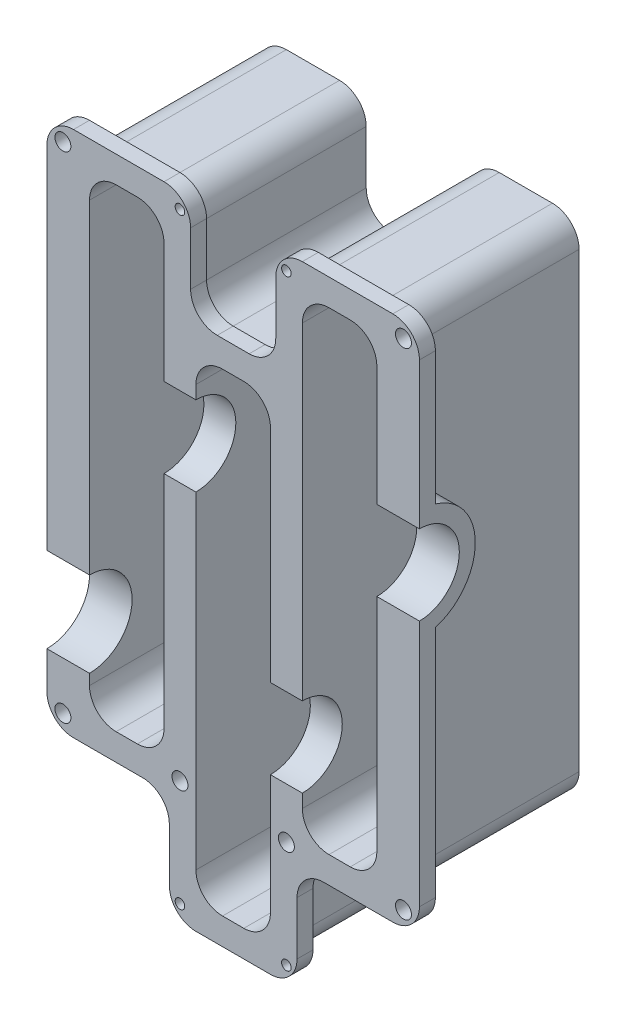
SolidWorks part; units mm, degrees
ref_plane "Front Plane" through (0, 0, 0) normal (0, 0, 1) x (1, 0, 0)
ref_plane "Top Plane" through (0, 0, 0) normal (0, 1, 0) x (1, 0, 0)
ref_plane "Right Plane" through (0, 0, 0) normal (1, 0, 0) x (0, 0, -1)
sketch "Sketch1" plane through (0, 0, 0) normal (0, 0, 1) x (1, 0, 0)
  line L1 (-35, 59.5) -> (35, 59.5)
  line L2 (-35, 59.5) -> (-35, -59.5)
  line L3 (-35, -59.5) -> (35, -59.5)
  line L4 (35, 59.5) -> (35, -59.5)
  line L5 (-35, 59.5) -> (35, -59.5) construction
  line L6 (-35, -59.5) -> (35, 59.5) construction
  point P0 (0, 0)
  dimension "D1" = 119
  dimension "D2" = 70
extrude "Boss-Extrude1" add sketch "Sketch1" along normal blind 35
sketch "Sketch2" plane through (-35, 0, 0) normal (-1, 0, 0) x (0, 0, 1)
  line L0 (35, 59.5) -> (35, -59.5) construction
  line L1 (35, -59.5) -> (0, -59.5) construction
  circle A0 centre (35, -19.5) radius 8
  dimension "D2" = 16
  dimension "D1" = 40
extrude "Cut-Extrude1" cut sketch "Sketch2" against normal blind 8
sketch "Sketch3" plane through (0, 0, 35) normal (0, 0, 1) x (1, 0, 0)
  line L0 (-35, 59.5) -> (-35, -11.5) construction
  line L1 (-27, 54.5) -> (-13, 54.5)
  line L2 (-27, 54.5) -> (-27, -34.5)
  line L3 (-27, -34.5) -> (-13, -34.5)
  line L4 (-13, 54.5) -> (-13, 27)
  line L5 (-7, 34.5) -> (7, 34.5)
  line L6 (-7, 34.5) -> (-7, 27)
  line L7 (-7, -54.5) -> (7, -54.5)
  line L8 (7, 34.5) -> (7, -12)
  line L9 (13, 54.5) -> (27, 54.5)
  line L10 (13, 54.5) -> (13, -12)
  line L11 (13, -34.5) -> (27, -34.5)
  line L12 (27, 54.5) -> (27, -34.5)
  line L13 (-35, -19.5) -> (40.8118, -19.5) construction
  line L14 (-35, -11.5) -> (-35, -27.5) construction
  line L15 (-41.2819, 19.5) -> (46.0892, 19.5) construction
  line L16 (-7, 27) -> (-13, 27)
  line L17 (-7, 12) -> (-13, 12)
  line L18 (-7, 12) -> (-7, -54.5)
  line L19 (-13, 12) -> (-13, -34.5)
  line L20 (7, -27) -> (13, -27)
  line L21 (7, -12) -> (13, -12)
  line L22 (13, -27) -> (13, -34.5)
  line L23 (7, -27) -> (7, -54.5)
  dimension "D1" = 8
  dimension "D2" = 14
  dimension "D3" = 6
  dimension "D4" = 6
  dimension "D5" = 39
  dimension "D6" = 15
  dimension "D7" = 89
  dimension "D8" = 15
  dimension "D9" = 7.5
  dimension "D10" = 15
  dimension "D11" = 7.5
  dimension "D12" = 15
  dimension "D13" = 89
extrude "Cut-Extrude2" cut sketch "Sketch3" against normal blind 32
sketch "Sketch4" plane through (35, 0, 0) normal (1, 0, 0) x (0, 0, -1)
  line L0 (-35, -59.5) -> (-35, 59.5) construction
  line L1 (-35, -59.5) -> (0, -59.5) construction
  circle A0 centre (-35, 19.5) radius 7.5
  dimension "D1" = 15
  dimension "D2" = 79
extrude "Cut-Extrude3" cut sketch "Sketch4" against normal blind 8
sketch "Sketch5" plane through (0, 0, 35) normal (0, 0, 1) x (1, 0, 0)
  line L0 (35, 59.5) -> (-35, 59.5) construction
  line L1 (8, 59.5) -> (-8, 59.5)
  line L2 (8, 59.5) -> (8, 39.5)
  line L3 (8, 39.5) -> (-8, 39.5)
  line L4 (-8, 59.5) -> (-8, 39.5)
  line L5 (-35, -27.5) -> (-35, -59.5) construction
  line L6 (-35, -39.5) -> (-12, -39.5)
  line L7 (-35, -39.5) -> (-35, -59.5)
  line L8 (-35, -59.5) -> (-12, -59.5)
  line L9 (-12, -39.5) -> (-12, -59.5)
  line L10 (-35, -59.5) -> (35, -59.5) construction
  line L11 (35, -59.5) -> (35, 12) construction
  line L12 (12, -59.5) -> (35, -59.5)
  line L13 (12, -59.5) -> (12, -39.5)
  line L14 (12, -39.5) -> (35, -39.5)
  line L15 (35, -59.5) -> (35, -39.5)
  line L16 (13, -34.5) -> (27, -34.5) construction
  line L17 (7, -54.5) -> (7, -27) construction
  line L18 (-27, -34.5) -> (-13, -34.5) construction
  line L19 (-7, 12) -> (-7, -54.5) construction
  line L20 (-13, 27) -> (-13, 54.5) construction
  line L21 (13, 54.5) -> (13, -12) construction
  line L22 (7, 34.5) -> (-7, 34.5) construction
  dimension "D1" = 5
  dimension "D2" = 5
  dimension "D3" = 5
  dimension "D4" = 5
  dimension "D5" = 5
  dimension "D6" = 5
  dimension "D7" = 5
extrude "Cut-Extrude4" cut sketch "Sketch5" against normal through all
sketch "Sketch6" plane through (-35, 0, 0) normal (-1, 0, 0) x (0, 0, 1)
  line L2 (0, -39.5) -> (0, 59.5)
  line L3 (0, 59.5) -> (32, 59.5)
  line L4 (32, -30.083) -> (32, -39.5)
  line L5 (32, 59.5) -> (32, -8.917)
  line L6 (32, -30.083) -> (32, -39.5)
  line L7 (32, 59.5) -> (32, -8.917)
  line L8 (32, -39.5) -> (0, -39.5)
  arc A2 (32, -8.917) -> (32, -30.083) centre (35, -19.5) ccw
  arc A3 (32, -8.917) -> (32, -30.083) centre (35, -19.5) ccw
  dimension "D1" = 3
extrude "Cut-Extrude5" cut sketch "Sketch6" against normal blind 5
sketch "Sketch7" plane through (0, -39.5, 0) normal (0, -1, 0) x (1, 0, 0)
  line L0 (-12, 0) -> (-12, 35) construction
  line L1 (-30, 32) -> (-12, 32)
  line L2 (-30, 32) -> (-30, 0)
  line L3 (-30, 0) -> (-12, 0)
  line L4 (-12, 32) -> (-12, 0)
  line L5 (-12, 0) -> (-12, 35) construction
extrude "Cut-Extrude6" cut sketch "Sketch7" against normal blind 2
sketch "Sketch8" plane through (-12, 0, 0) normal (-1, 0, 0) x (0, 0, 1)
  line L0 (0, -59.5) -> (0, -37.5) construction
  line L1 (32, -37.5) -> (0, -37.5)
  line L2 (32, -37.5) -> (32, -59.5)
  line L3 (32, -59.5) -> (0, -59.5)
  line L4 (0, -37.5) -> (0, -59.5)
extrude "Cut-Extrude7" cut sketch "Sketch8" against normal blind 2
sketch "Sketch9" plane through (0, -59.5, 0) normal (0, -1, 0) x (1, 0, 0)
  line L1 (-10, 32) -> (12, 32)
  line L2 (-10, 32) -> (-10, 0)
  line L3 (-10, 0) -> (12, 0)
  line L4 (12, 32) -> (12, 0)
extrude "Cut-Extrude8" cut sketch "Sketch9" against normal blind 2
sketch "Sketch10" plane through (12, 0, 0) normal (1, 0, 0) x (0, 0, -1)
  line L1 (-32, -57.5) -> (0, -57.5)
  line L2 (-32, -57.5) -> (-32, -39.5)
  line L3 (-32, -39.5) -> (0, -39.5)
  line L4 (0, -57.5) -> (0, -39.5)
extrude "Cut-Extrude9" cut sketch "Sketch10" against normal blind 2
sketch "Sketch11" plane through (0, -39.5, 0) normal (0, -1, 0) x (1, 0, 0)
  line L1 (10, 32) -> (35, 32)
  line L2 (10, 32) -> (10, 0)
  line L3 (10, 0) -> (35, 0)
  line L4 (35, 32) -> (35, 0)
extrude "Cut-Extrude10" cut sketch "Sketch11" against normal blind 2
sketch "Sketch12" plane through (35, 0, 0) normal (1, 0, 0) x (0, 0, -1)
  line L2 (-32, 59.5) -> (0, 59.5)
  line L3 (0, 59.5) -> (0, -37.5)
  line L4 (-32, 29.5623) -> (-32, 59.5)
  line L5 (-32, -39.5) -> (-32, 9.4377)
  line L6 (-32, 29.5623) -> (-32, 59.5)
  line L7 (-32, -37.5) -> (-32, 9.4377)
  line L8 (0, -37.5) -> (-32, -37.5)
  arc A2 (-32, 9.4377) -> (-32, 29.5623) centre (-35, 19.5) ccw
  arc A3 (-32, 9.4377) -> (-32, 29.5623) centre (-35, 19.5) ccw
  dimension "D1" = 3
extrude "Cut-Extrude11" cut sketch "Sketch12" against normal blind 5
sketch "Sketch13" plane through (0, 59.5, 0) normal (0, 1, 0) x (1, 0, 0)
  line L1 (30, -32) -> (8, -32)
  line L2 (30, -32) -> (30, 0)
  line L3 (30, 0) -> (8, 0)
  line L4 (8, -32) -> (8, 0)
extrude "Cut-Extrude12" cut sketch "Sketch13" against normal blind 2
sketch "Sketch14" plane through (8, 0, 0) normal (-1, 0, 0) x (0, 0, 1)
  line L0 (32, -8.917) -> (32, 59.5) construction
  line L1 (32, 57.5) -> (0, 57.5)
  line L2 (32, 57.5) -> (32, 39.5)
  line L3 (32, 39.5) -> (0, 39.5)
  line L4 (0, 57.5) -> (0, 39.5)
  line L5 (0, 39.5) -> (35, 39.5) construction
  point P8 (0, 57.5)
extrude "Cut-Extrude17" cut sketch "Sketch14" against normal blind 2
sketch "Sketch18" plane through (0, 39.5, 0) normal (0, 1, 0) x (1, 0, 0)
  line L1 (-8, 0) -> (10, 0)
  line L2 (-8, 0) -> (-8, -32)
  line L3 (-8, -32) -> (10, -32)
  line L4 (10, 0) -> (10, -32)
extrude "Cut-Extrude18" cut sketch "Sketch18" against normal blind 2
sketch "Sketch20" plane through (-8, 0, 0) normal (1, 0, 0) x (0, 0, -1)
  line L1 (-32, 37.5) -> (0, 37.5)
  line L2 (-32, 37.5) -> (-32, 59.5)
  line L3 (-32, 59.5) -> (0, 59.5)
  line L4 (0, 37.5) -> (0, 59.5)
extrude "Cut-Extrude19" cut sketch "Sketch20" against normal blind 2
sketch "Sketch21" plane through (0, 59.5, 0) normal (0, 1, 0) x (1, 0, 0)
  line L1 (-10, -32) -> (-30, -32)
  line L2 (-10, -32) -> (-10, 0)
  line L3 (-10, 0) -> (-30, 0)
  line L4 (-30, -32) -> (-30, 0)
extrude "Cut-Extrude20" cut sketch "Sketch21" against normal blind 2
fillet "Fillet1" radius 5 12 edges at (-7, 34.5, 19) (7, 34.5, 19) (-13, -34.5, 19) (7, -54.5, 19) (27, -34.5, 19) (13, -34.5, 19) (-7, -54.5, 19) (-27, -34.5, 19) (13, 54.5, 19) (27, 54.5, 19) (-13, 54.5, 19) (-27, 54.5, 19)
fillet "Fillet2" radius 5 12 edges at (-35, -39.5, 33.5) (-12, -39.5, 33.5) (-12, -59.5, 33.5) (12, -59.5, 33.5) (12, -39.5, 33.5) (35, -39.5, 33.5) (10, -37.5, 16) (10, -57.5, 16) (-10, -57.5, 16) (-10, -37.5, 16) (-30, -37.5, 16) (30, -37.5, 16)
fillet "Fillet3" radius 5 12 edges at (30, 57.5, 16) (10, 57.5, 16) (10, 37.5, 16) (-10, 37.5, 16) (-10, 57.5, 16) (-30, 57.5, 16) (8, 39.5, 33.5) (-8, 39.5, 33.5) (-35, 59.5, 33.5) (-8, 59.5, 33.5) (8, 59.5, 33.5) (35, 59.5, 33.5)
sketch "Sketch23" plane through (0, 0, 35) normal (0, 0, 1) x (1, 0, 0)
  line L0 (-13, 59.5) -> (-30, 59.5) construction
  line L1 (-32, 56.5) -> (32, 56.5) construction
  line L2 (-32, 56.5) -> (-32, -36.5) construction
  line L3 (-32, -36.5) -> (32, -36.5) construction
  line L4 (32, 56.5) -> (32, -36.5) construction
  line L5 (-35, 54.5) -> (-35, -11.5) construction
  line L6 (-7, 12) -> (-7, -49.5) construction
  line L7 (7, -49.5) -> (7, -27) construction
  circle A0 centre (-32, 56.5) radius 1.5
  circle A1 centre (32, 56.5) radius 1.5
  circle A2 centre (-32, -36.5) radius 1.5
  circle A3 centre (32, -36.5) radius 1.5
  circle A4 centre (-10, -36.5) radius 1.5
  circle A5 centre (10, -36.5) radius 1.5
  dimension "D7" = 3
  dimension "D1" = 93
  dimension "D2" = 64
  dimension "D3" = 3
  dimension "D4" = 3
  dimension "D5" = 3
  dimension "D6" = 3
extrude "Cut-Extrude21" cut sketch "Sketch23" against normal blind 10
sketch "Sketch24" plane through (0, 0, 35) normal (0, 0, 1) x (1, 0, 0)
  line L0 (-8, 54.5) -> (-8, 44.5) construction
  line L1 (-10, 56.5) -> (10, 56.5) construction
  line L2 (-10, 56.5) -> (-10, -56.5) construction
  line L3 (-10, -56.5) -> (10, -56.5) construction
  line L4 (10, 56.5) -> (10, -56.5) construction
  line L5 (30, 59.5) -> (13, 59.5) construction
  circle A0 centre (-10, 56.5) radius 0.9
  circle A1 centre (10, 56.5) radius 0.9
  circle A2 centre (-10, -56.5) radius 0.9
  circle A3 centre (10, -56.5) radius 0.9
  dimension "D5" = 1.8
  dimension "D1" = 113
  dimension "D2" = 20
  dimension "D3" = 2
  dimension "D4" = 3
extrude "Cut-Extrude22" cut sketch "Sketch24" against normal blind 10
sketch "Sketch25" plane through (-13, 0, 0) normal (-1, 0, 0) x (0, 0, 1)
  line L0 (35, 27) -> (3, 27)
  line L1 (3, 27) -> (3, 12)
  line L2 (3, 12) -> (35, 12)
  line L3 (3, 27) -> (35, 27) construction
  line L5 (35, -29.5) -> (35, 12) construction
  arc A0 (35, 27) -> (35, 12) centre (35, 19.5) ccw
  point P7 (0, 0)
  point P9 (35, 29.2603)
  dimension "D1" = 15
  dimension "D2" = 32
  dimension "D3" = 0
  dimension "D4" = 0
extrude "Boss-Extrude2" add sketch "Sketch25" against normal blind 6
sketch "Sketch26" plane through (7, 0, 0) normal (-1, 0, 0) x (0, 0, 1)
  line L0 (35, -12) -> (3, -12)
  line L1 (3, -12) -> (3, -27)
  line L2 (3, -27) -> (35, -27)
  arc A0 (35, -12) -> (35, -27) centre (35, -19.5) ccw
  dimension "D1" = 15
  dimension "D2" = 32
extrude "Boss-Extrude3" add sketch "Sketch26" against normal blind 6
